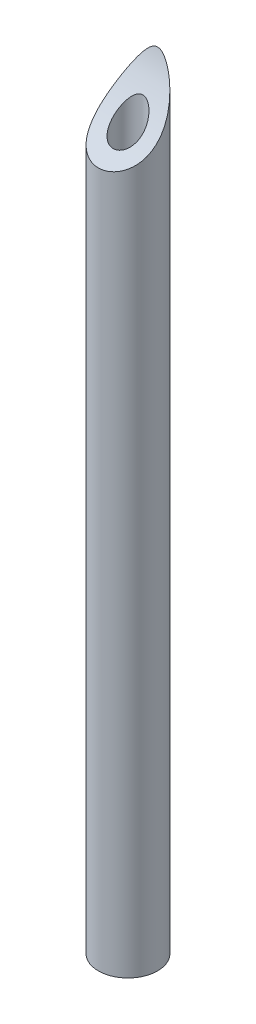
SolidWorks part; units mm, degrees
material "PTFE (general)"
ref_plane "Front Plane" through (0, 0, 0) normal (0, 0, 1) x (1, 0, 0)
ref_plane "Top Plane" through (0, 0, 0) normal (0, 1, 0) x (1, 0, 0)
ref_plane "Right Plane" through (0, 0, 0) normal (1, 0, 0) x (0, 0, -1)
sketch "Sketch1" plane through (0, 0, 0) normal (0, 1, 0) x (1, 0, 0)
  circle A0 centre (0, 0) radius 2
  circle A1 centre (0, 0) radius 1
  dimension "D1" = 4
  dimension "D2" = 2
extrude "Boss-Extrude1" add sketch "Sketch1" along normal mid plane 52 contours A0
sketch "Sketch2" plane through (0, 0, 0) normal (1, 0, 0) x (0, 0, -1)
  line L1 (2, 26) -> (-2, 26) construction
  circle A0 centre (-5.746, 28) radius 8
  dimension "D1" = 16
  dimension "D2" = 2
extrude "Cut-Extrude1" cut sketch "Sketch2" against normal mid plane 4
